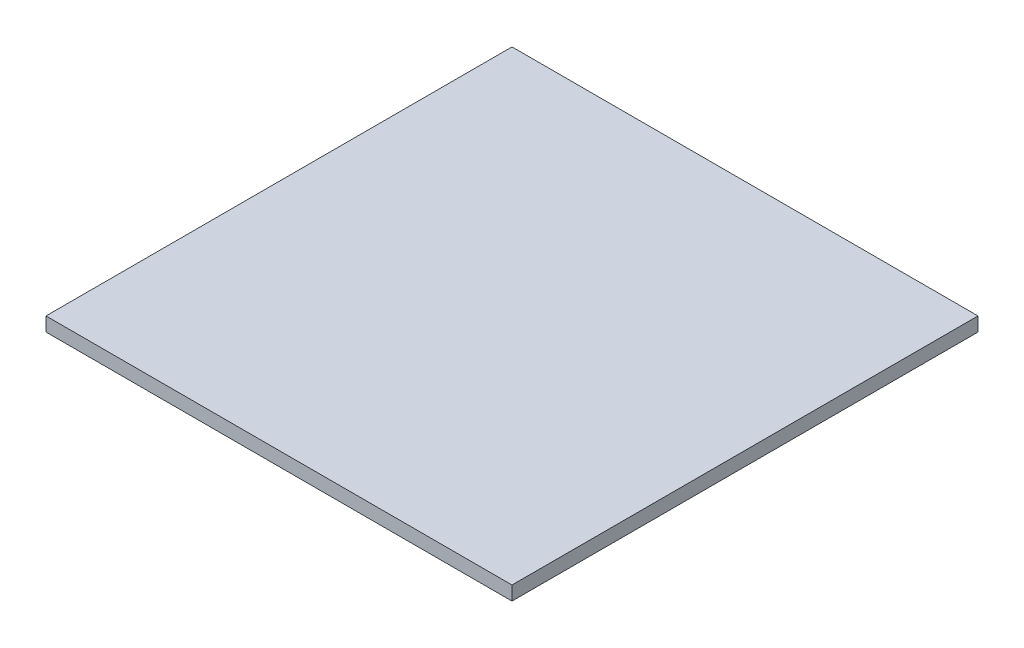
SolidWorks part; units mm, degrees
ref_plane "Спереди" through (0, 0, 0) normal (0, 0, 1) x (1, 0, 0)
ref_plane "Сверху" through (0, 0, 0) normal (0, 1, 0) x (1, 0, 0)
ref_plane "Справа" through (0, 0, 0) normal (1, 0, 0) x (0, 0, -1)
other "Configuration Table"
sketch "Эскиз1" plane through (0, 0, 0) normal (0, 1, 0) x (1, 0, 0)
  line L1 (-80.2632, 43.75) -> (19.7368, 43.75)
  line L2 (-80.2632, 43.75) -> (-80.2632, -56.25)
  line L3 (-80.2632, -56.25) -> (19.7368, -56.25)
  line L4 (19.7368, 43.75) -> (19.7368, -56.25)
  dimension "D1" = 100
  dimension "D2" = 100
extrude "Бобышка-Вытянуть1" add sketch "Эскиз1" along normal blind 3
